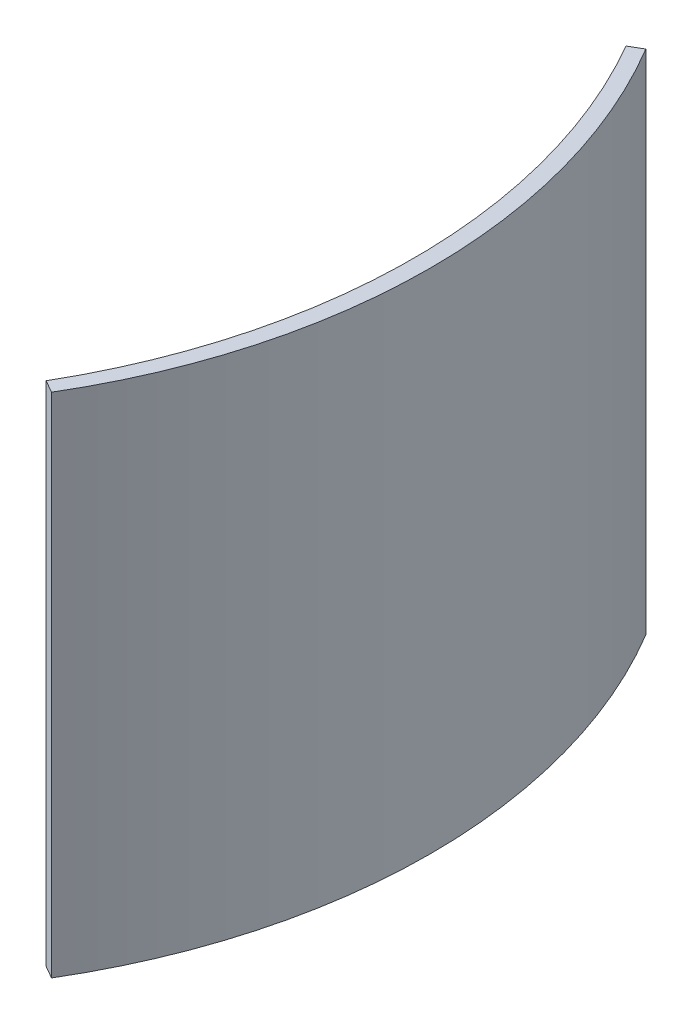
SolidWorks part; units mm, degrees
ref_plane "Front Plane" through (0, 0, 0) normal (0, 0, 1) x (1, 0, 0)
ref_plane "Top Plane" through (0, 0, 0) normal (0, 1, 0) x (1, 0, 0)
ref_plane "Right Plane" through (0, 0, 0) normal (1, 0, 0) x (0, 0, -1)
sketch "Sketch1" plane through (0, 0, 0) normal (0, 1, 0) x (1, 0, 0)
  line L2 (0, 0) -> (0, -40) construction
  line L3 (0, 0) -> (0.866, 0.5)
  line L4 (0, -40) -> (0.866, -40.5)
  arc A2 (0, 0) -> (0, -40) centre (-34.641, -20) cw
  arc A3 (0.866, 0.5) -> (0.866, -40.5) centre (-33.4815, -20) cw
  dimension "D3" = 1
  dimension "D2" = 40
  dimension "D5" = 40
  dimension "D1" = 40
  dimension "D4" = 1
extrude "Boss-Extrude1" add sketch "Sketch1" along normal blind 35
sketch "Sketch2" plane through (0, 35, 0) normal (0, 1, 0) x (1, 0, 0)
  arc A0 (0.866, -40.5) -> (0.866, 0.5) centre (-33.4815, -20) ccw construction
  point P0 (6.5185, -20)
